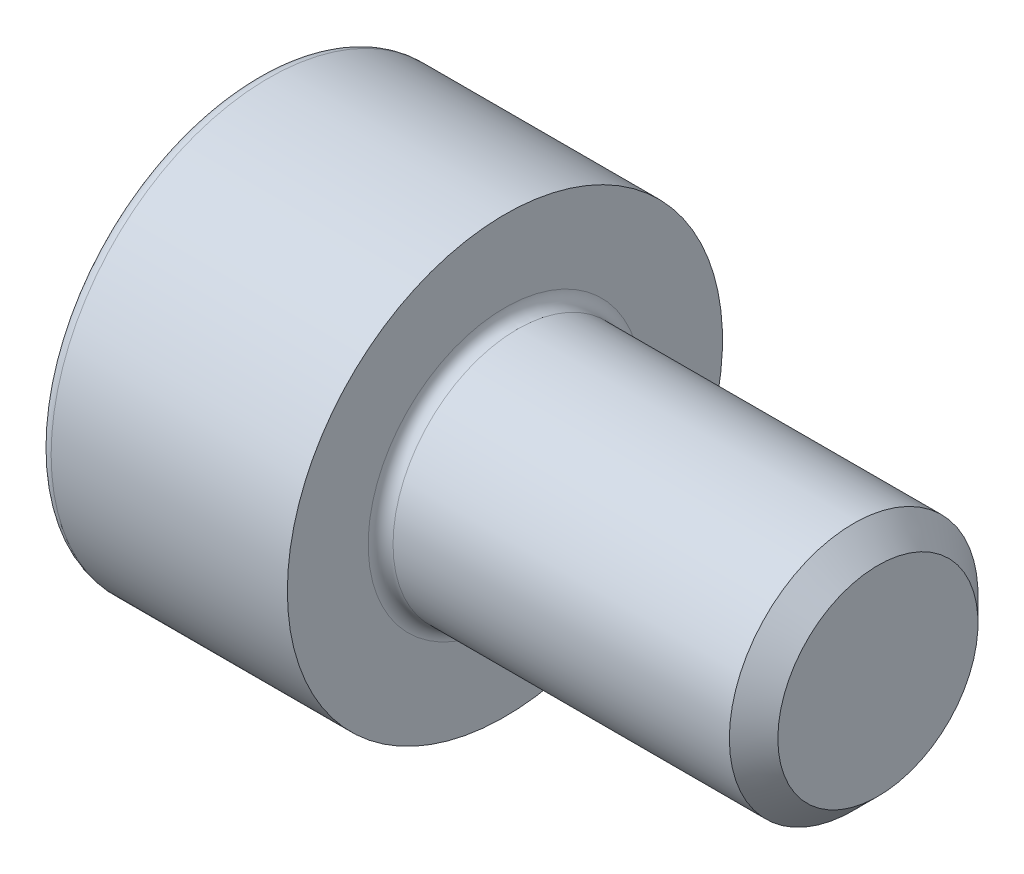
SolidWorks part; units mm, degrees
revolve "Base-Revolve" add sketch "BodySke"
sketch "BodySke" plane through (0, 0, 0) normal (0, 0, 1) x (1, 0, 0)
  line L0 (0, 0) -> (0, 3.5)
  line L1 (0, 3.5) -> (4, 3.5)
  line L2 (4, 3.5) -> (4, 2)
  line L3 (4, 2) -> (9.61, 2)
  line L4 (10, 1.61) -> (10, 0)
  line L5 (10, 0) -> (0, 0)
  line L6 (-31.75, 0) -> (127, 0) construction
  line L8 (10, 1.61) -> (9.61, 2)
  line L10 (10, -1.61) -> (9.61, -2) construction
  line L11 (4.7, 9.525) -> (4.7, 3.175) construction
  line L12 (4, 9.525) -> (4, 3.175) construction
  line L13 (-50, 9.525) -> (-50, 3.175) construction
  dimension "Head_ht" = 4
  dimension "Length" = 6
  dimension "Body_ch_ang" = 45
  dimension "Diameter" = 4
  dimension "Minor_dia" = 3.22
  dimension "Advance" = 0.7
  dimension "Thread_nom" = 6
  dimension "Thread_length" = 60
  dimension "Head_dia" = 7
cosmetic thread "ThreadCosmetic" [suppressed]
fillet "Fillet1" radius 0.2 1 edges at (4, 0, 2)
fillet "Fillet2" radius 0.2 1 edges at (0, 0, 3.5)
ref_plane "Plane1" through (0, 0, 0) normal (0, 0, 1) x (1, 0, 0)
ref_plane "Plane2" through (0, 0, 0) normal (0, 1, 0) x (1, 0, 0)
ref_plane "Plane3" through (0, 0, 0) normal (1, 0, 0) x (0, 0, -1)
sketch "Sketch2" plane through (0, 0, 0) normal (0, 0, 1) x (1, 0, 0)
  line L0 (0, 1.5355) -> (2, 1.5355)
  line L1 (2, 1.5355) -> (2.8865, 0)
  line L2 (-31.75, 0) -> (127, 0) construction
  line L3 (2.8865, 0) -> (0, 0)
  line L4 (0, 0) -> (0, 1.5355)
  line L6 (0, 0) -> (47.625, 0) construction
  dimension "D1" = 1.5355
  dimension "D2" = 60
  dimension "Depth" = 2
revolve "Hex-PreBroach" cut sketch "Sketch2" angle 360 about L6
sketch "Sketch3" plane through (0, 0, 0) normal (-1, 0, 0) x (0, 0.5, 0.866)
  line L0 (0.8865, 1.5355) -> (-0.8865, 1.5355)
  line L1 (-0.8865, 1.5355) -> (-1.773, 0)
  line L2 (0.8865, 1.5355) -> (1.773, 0)
  line L3 (0.8865, -1.5355) -> (1.773, 0)
  line L4 (0.8865, -1.5355) -> (-0.8865, -1.5355)
  line L5 (-0.8865, -1.5355) -> (-1.773, 0)
  dimension "D1" = 1.5355
  dimension "D2" = 1.5355
  dimension "Hex_size" = 3.071
extrude "Hex" cut sketch "Sketch3" against normal blind 2
sketch "ThdSchSke" plane through (0, 0, 0) normal (0, 0, 1) x (1, 0, 0)
  line L0 (6.1, -1.61) -> (5.8269, -2)
  line L1 (6.1, -1.61) -> (6.3731, -2)
  line L2 (6.3731, -2) -> (6.3731, -2.5)
  line L3 (-3.175, 0) -> (5.1513, 0) construction
  line L4 (0, 3.3) -> (0, -3.3) construction
  line L5 (6.3731, -2.5) -> (5.8269, -2.5)
  line L6 (5.8269, -2.5) -> (5.8269, -2)
  dimension "Thread_minor" = 3.22
  dimension "Diameter" = 4
  dimension "Start" = 6.1
revolve "ThreadSchematic" [suppressed] cut sketch "ThdSchSke" angle 360 about L3
pattern_linear "ThdSchPat" [suppressed]
equation "\"D2@Sketch3\" = \"Hex_size@Sketch3\" / 2"
equation "\"D1@Sketch3\" = \"Hex_size@Sketch3\" / 2"
equation "\"D1@Sketch2\" = \"Hex_size@Sketch3\" / 2"
equation "\"Thread_minor@ThreadCosmetic\"  =  \"Minor_dia@BodySke\""
equation "\"Depth@Sketch2\" =  \"Key_eng@Hex\""
equation "\"Thread_length@ThreadCosmetic\" = ((sgn( (\"Length@BodySke\" - \"Advance@BodySke\" * 3.0) - \"Thread_nom@BodySke\" )-1)*( (\"Length@BodySke\" - \"Advance@BodySke\" * 3.0) - \"Thread_nom@BodySke\" ))/-2+ \"Thread_nom@BodySke\""
equation "\"Thread_minor@ThdSchSke\" = \"Minor_dia@BodySke\""
equation "\"Diameter@ThdSchSke\" = \"Diameter@BodySke\""
equation "\"Overcut@ThdSchSke\" = \"Diameter@BodySke\" * 1.25"
equation "\"Start@ThdSchSke\" = \"Head_ht@BodySke\" + \"Length@BodySke\" - \"Thread_length@ThreadCosmetic\"  '---Non-countersunk---"
equation "\"Num_threads@ThdSchPat\" = int( \"Thread_length@ThreadCosmetic\" / \"Advance@BodySke\" + 0.999 )  + 1"
equation "\"Advance@ThdSchPat\" = \"Thread_length@ThreadCosmetic\" /  (\"Num_threads@ThdSchPat\" - 1) 'relax it"
equation "\"Num_threads@ThdSchPat\" = \"Num_threads@ThdSchPat\" - sgn( \"Num_threads@ThdSchPat\" - 1) '---chamfered tips only---"
